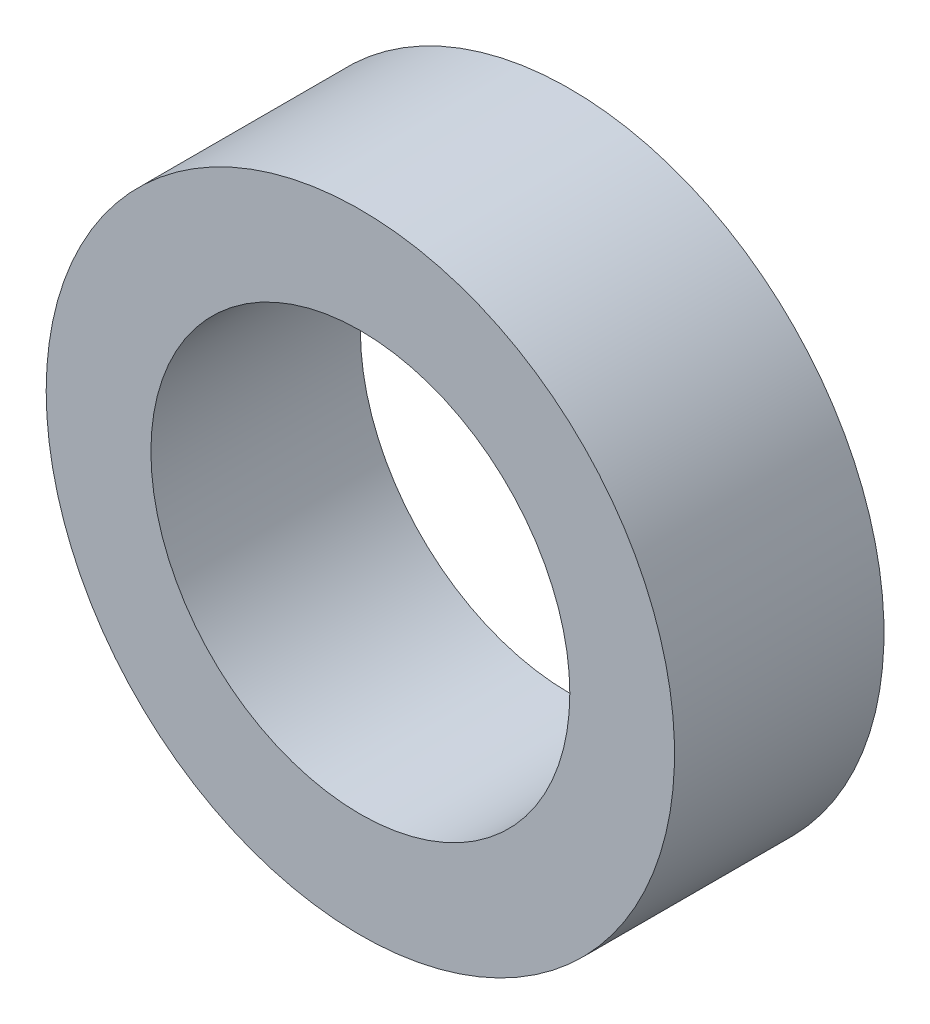
SolidWorks part; units mm, degrees
ref_plane "Plane1" through (0, 0, 0) normal (0, 0, 1) x (1, 0, 0)
ref_plane "Plane2" through (0, 0, 0) normal (0, 1, 0) x (1, 0, 0)
ref_plane "Plane3" through (0, 0, 0) normal (1, 0, 0) x (0, 0, -1)
sketch "Эскиз1" plane through (0, 0, 0) normal (0, 0, 1) x (1, 0, 0)
  arc A0 (-40, 0) -> (-50, 10) centre (-40, 10) cw
  arc A1 (-50, 10) -> (-40, 0) centre (-40, 10) cw
  dimension "D1" = 10
extrude "Вытянуть-Тонкостенный1" add sketch "Эскиз1" along normal blind 10 thin thin type one direction wall 5
